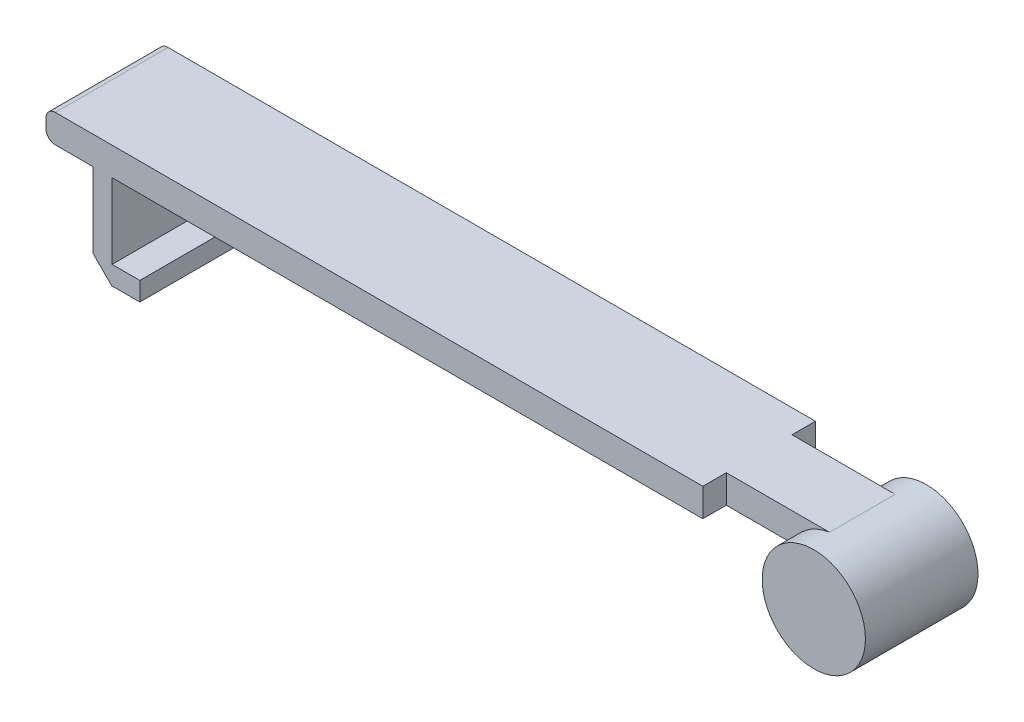
SolidWorks part; units mm, degrees
ref_plane "Plan de face" through (0, 0, 0) normal (0, 0, 1) x (1, 0, 0)
ref_plane "Plan de dessus" through (0, 0, 0) normal (0, 1, 0) x (1, 0, 0)
ref_plane "Plan de droite" through (0, 0, 0) normal (1, 0, 0) x (0, 0, -1)
sketch "Esquisse1" plane through (0, 0, 0) normal (0, 0, 1) x (1, 0, 0)
  circle A0 centre (25.4772, 0.4062) radius 5.5
  dimension "D1" = 11
extrude "Boss.-Extru.1" add sketch "Esquisse1" along normal blind 12
ref_plane "Plan1" through (0, 0, 2.5) normal (0, 0, 1) x (1, 0, 0)
sketch "Esquisse2" plane through (0, 0, 2.5) normal (0, 0, 1) x (1, 0, 0)
  line L1 (25.6544, 5.8437) -> (13.6544, 5.8437)
  line L2 (25.6544, 5.8437) -> (25.6544, 2.8437)
  line L3 (25.6544, 2.8437) -> (13.6544, 2.8437)
  line L4 (13.6544, 5.8437) -> (13.6544, 2.8437)
  dimension "D1" = 12
  dimension "D2" = 3
extrude "Boss.-Extru.2" add sketch "Esquisse2" along normal blind 7
sketch "Esquisse3" plane through (0, 0, 0) normal (0, 0, 1) x (1, 0, 0)
  line L1 (13.6544, 2.8437) -> (-51.3456, 2.8437)
  line L2 (13.6544, 2.8437) -> (13.6544, 5.8437)
  line L3 (13.6544, 5.8437) -> (-51.3456, 5.8437)
  line L4 (-51.3456, 2.8437) -> (-51.3456, 5.8437)
  line L5 (-51.3456, 2.8437) -> (-51.3456, -7.1563)
  line L6 (-51.3456, -7.1563) -> (-46.3456, -7.1563)
  line L7 (-46.3456, -7.1563) -> (-46.3456, -5.1563)
  line L8 (-46.3456, -5.1563) -> (-49.2982, -5.1563)
  line L9 (-49.2982, -5.1563) -> (-49.2982, 2.8437)
  line L10 (-49.2982, 2.8437) -> (-51.3456, 2.8437)
  line L11 (-51.3456, 5.8437) -> (-56.3456, 5.8437)
  line L12 (-56.3456, 5.8437) -> (-56.3456, 2.8437)
  line L13 (-56.3456, 2.8437) -> (-51.3456, 2.8437)
  dimension "D1" = 65
  dimension "D2" = 5
  dimension "D3" = 2
  dimension "D4" = 8
  dimension "D5" = 3
  dimension "D6" = 5
extrude "Boss.-Extru.3" add sketch "Esquisse3" along normal blind 12 contours L8 L9 L1 L5 L6 L7 | L12 L13 L4 L11
chamfer "Chanfrein1" distance 2 angle 45 1 edges at (-51.3456, -7.1563, 6)
fillet "Congé1" radius 1 2 edges at (-56.3456, 2.8437, 6) (-56.3456, 5.8437, 6)
